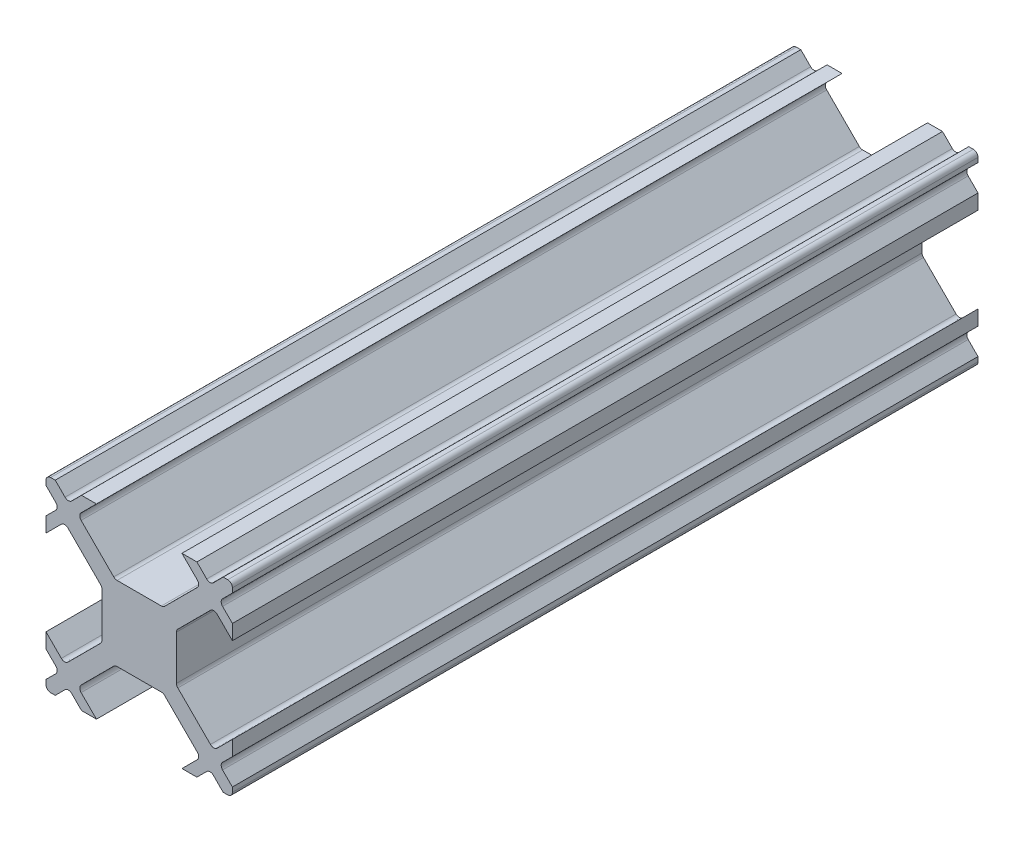
SolidWorks part; units mm, degrees
material "6063-T6"
ref_plane "Front Plane" through (0, 0, 0) normal (0, 0, 1) x (1, 0, 0)
ref_plane "Top Plane" through (0, 0, 0) normal (0, 1, 0) x (1, 0, 0)
ref_plane "Right Plane" through (0, 0, 0) normal (1, 0, 0) x (0, 0, -1)
ref_plane "Plane1" through (0, 0, 12.5) normal (0, 0, 1) x (1, 0, 0)
sketch "Sketch1" plane through (0, 0, 12.5) normal (0, 0, 1) x (1, 0, 0)
  line L0 (1.1893, 2) -> (-1.1893, 2)
  line L1 (-1.3661, 2.0732) -> (-3.1161, 3.8232)
  line L2 (-3.1161, 4.1768) -> (-2.2929, 5)
  line L3 (-2.2929, 5) -> (-3.095, 5)
  line L4 (-3.095, 5) -> (-3.6232, 4.4718)
  line L5 (-3.9768, 4.4718) -> (-4.505, 5)
  line L6 (-4.505, 5) -> (-4.75, 5)
  line L7 (-5, 4.75) -> (-5, 4.505)
  line L8 (-5, 4.505) -> (-4.4718, 3.9768)
  line L9 (-4.4718, 3.6232) -> (-5, 3.095)
  line L10 (-5, 3.095) -> (-5, 2.2929)
  line L11 (-5, 2.2929) -> (-4.1768, 3.1161)
  line L12 (-3.8232, 3.1161) -> (-2.0732, 1.3661)
  line L13 (-2, 1.1893) -> (-2, -1.1893)
  line L14 (-2.0732, -1.3661) -> (-3.8232, -3.1161)
  line L15 (-4.1768, -3.1161) -> (-5, -2.2929)
  line L16 (-5, -2.2929) -> (-5, -3.095)
  line L17 (-5, -3.095) -> (-4.4718, -3.6232)
  line L18 (-4.4718, -3.9768) -> (-5, -4.505)
  line L19 (-5, -4.505) -> (-5, -4.75)
  line L20 (-4.75, -5) -> (-4.505, -5)
  line L21 (-4.505, -5) -> (-3.9768, -4.4718)
  line L22 (-3.6232, -4.4718) -> (-3.095, -5)
  line L23 (-3.095, -5) -> (-2.2929, -5)
  line L24 (-2.2929, -5) -> (-3.1161, -4.1768)
  line L25 (-3.1161, -3.8232) -> (-1.3661, -2.0732)
  line L26 (-1.1893, -2) -> (1.1893, -2)
  line L27 (1.3661, -2.0732) -> (3.1161, -3.8232)
  line L28 (3.1161, -4.1768) -> (2.2929, -5)
  line L29 (2.2929, -5) -> (3.095, -5)
  line L30 (3.095, -5) -> (3.6232, -4.4718)
  line L31 (3.9768, -4.4718) -> (4.505, -5)
  line L32 (4.505, -5) -> (4.75, -5)
  line L33 (5, -4.75) -> (5, -4.505)
  line L34 (5, -4.505) -> (4.4718, -3.9768)
  line L35 (4.4718, -3.6232) -> (5, -3.095)
  line L36 (5, -3.095) -> (5, -2.2929)
  line L37 (5, -2.2929) -> (4.1768, -3.1161)
  line L38 (3.8232, -3.1161) -> (2.0732, -1.3661)
  line L39 (2, -1.1893) -> (2, 1.1893)
  line L40 (2.0732, 1.3661) -> (3.8232, 3.1161)
  line L41 (4.1768, 3.1161) -> (5, 2.2929)
  line L42 (5, 2.2929) -> (5, 3.095)
  line L43 (5, 3.095) -> (4.4718, 3.6232)
  line L44 (4.4718, 3.9768) -> (5, 4.505)
  line L45 (5, 4.505) -> (5, 4.75)
  line L46 (4.75, 5) -> (4.505, 5)
  line L47 (4.505, 5) -> (3.9768, 4.4718)
  line L48 (3.6232, 4.4718) -> (3.095, 5)
  line L49 (3.095, 5) -> (2.2929, 5)
  line L50 (2.2929, 5) -> (3.1161, 4.1768)
  line L51 (3.1161, 3.8232) -> (1.3661, 2.0732)
  arc A0 (1.3661, 2.0732) -> (1.1893, 2) centre (1.1893, 2.25) cw
  arc A1 (-1.1893, 2) -> (-1.3661, 2.0732) centre (-1.1893, 2.25) cw
  arc A2 (-3.1161, 3.8232) -> (-3.1161, 4.1768) centre (-2.9393, 4) cw
  arc A3 (-3.6232, 4.4718) -> (-3.9768, 4.4718) centre (-3.8, 4.6485) cw
  arc A4 (-4.75, 5) -> (-5, 4.75) centre (-4.75, 4.75) ccw
  arc A5 (-4.4718, 3.9768) -> (-4.4718, 3.6232) centre (-4.6485, 3.8) cw
  arc A6 (-4.1768, 3.1161) -> (-3.8232, 3.1161) centre (-4, 2.9393) cw
  arc A7 (-2.0732, 1.3661) -> (-2, 1.1893) centre (-2.25, 1.1893) cw
  arc A8 (-2, -1.1893) -> (-2.0732, -1.3661) centre (-2.25, -1.1893) cw
  arc A9 (-3.8232, -3.1161) -> (-4.1768, -3.1161) centre (-4, -2.9393) cw
  arc A10 (-4.4718, -3.6232) -> (-4.4718, -3.9768) centre (-4.6485, -3.8) cw
  arc A11 (-5, -4.75) -> (-4.75, -5) centre (-4.75, -4.75) ccw
  arc A12 (-3.9768, -4.4718) -> (-3.6232, -4.4718) centre (-3.8, -4.6485) cw
  arc A13 (-3.1161, -4.1768) -> (-3.1161, -3.8232) centre (-2.9393, -4) cw
  arc A14 (-1.3661, -2.0732) -> (-1.1893, -2) centre (-1.1893, -2.25) cw
  arc A15 (1.1893, -2) -> (1.3661, -2.0732) centre (1.1893, -2.25) cw
  arc A16 (3.1161, -3.8232) -> (3.1161, -4.1768) centre (2.9393, -4) cw
  arc A17 (3.6232, -4.4718) -> (3.9768, -4.4718) centre (3.8, -4.6485) cw
  arc A18 (4.75, -5) -> (5, -4.75) centre (4.75, -4.75) ccw
  arc A19 (4.4718, -3.9768) -> (4.4718, -3.6232) centre (4.6485, -3.8) cw
  arc A20 (4.1768, -3.1161) -> (3.8232, -3.1161) centre (4, -2.9393) cw
  arc A21 (2.0732, -1.3661) -> (2, -1.1893) centre (2.25, -1.1893) cw
  arc A22 (2, 1.1893) -> (2.0732, 1.3661) centre (2.25, 1.1893) cw
  arc A23 (3.8232, 3.1161) -> (4.1768, 3.1161) centre (4, 2.9393) cw
  arc A24 (4.4718, 3.6232) -> (4.4718, 3.9768) centre (4.6485, 3.8) cw
  arc A25 (5, 4.75) -> (4.75, 5) centre (4.75, 4.75) ccw
  arc A26 (3.9768, 4.4718) -> (3.6232, 4.4718) centre (3.8, 4.6485) cw
  arc A27 (3.1161, 4.1768) -> (3.1161, 3.8232) centre (2.9393, 4) cw
extrude "Boss-Extrude1" add sketch "Sketch1" against normal blind 40
